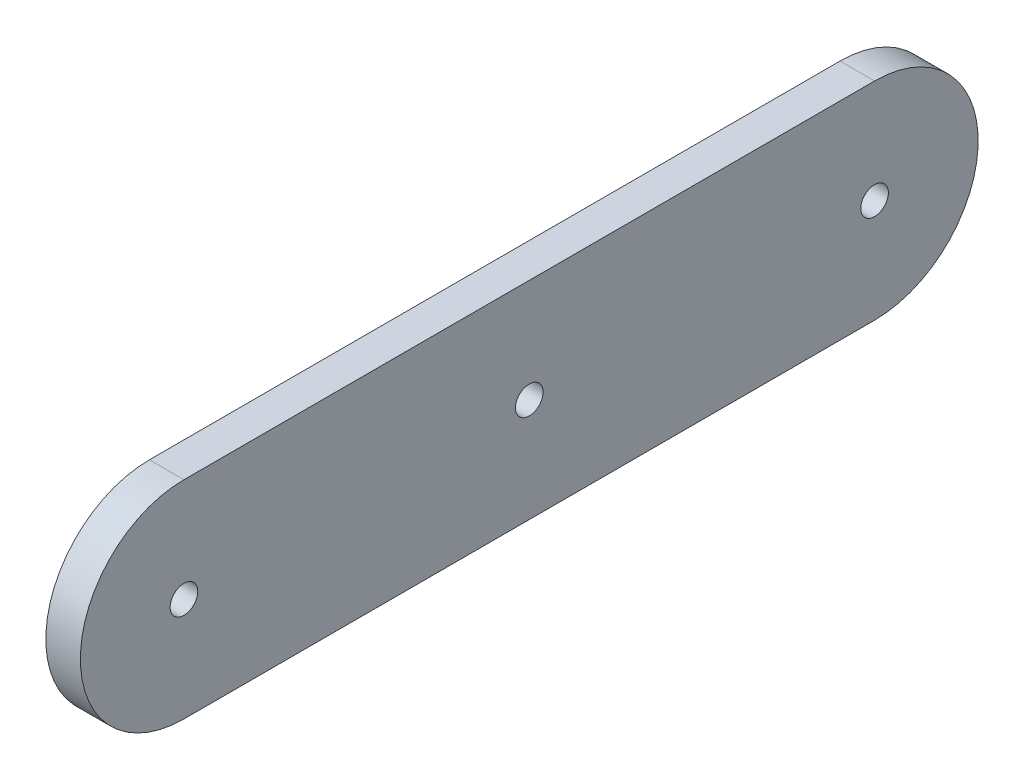
SolidWorks part; units mm, degrees
material "PMMA"
ref_plane "Front Plane" through (0, 0, 0) normal (0, 0, 1) x (1, 0, 0)
ref_plane "Top Plane" through (0, 0, 0) normal (0, 1, 0) x (1, 0, 0)
ref_plane "Right Plane" through (0, 0, 0) normal (1, 0, 0) x (0, 0, -1)
sketch "Schizzo1" plane through (0, 0, 0) normal (1, 0, 0) x (0, 0, -1)
  line L0 (-50, 15) -> (50, -15) construction
  line L1 (-50, 15) -> (50, 15)
  line L2 (-50, 15) -> (-50, -15) construction
  line L3 (-50, -15) -> (50, -15)
  line L4 (50, 15) -> (50, -15) construction
  arc A0 (-50, 15) -> (-50, -15) centre (-50, 0) ccw
  arc A1 (50, 15) -> (50, -15) centre (50, 0) cw
  point P4 (0, 0)
  dimension "D3" = 15
  dimension "D4" = 15
  dimension "D1" = 100
  dimension "D2" = 30
extrude "Estrusione-Estrusione1" add sketch "Schizzo1" along normal blind 5
sketch "Schizzo2" plane through (5, 0, 0) normal (1, 0, 0) x (0, 0, -1)
  circle A0 centre (-50, 0) radius 2
  circle A1 centre (0, 0) radius 2
  circle A2 centre (50, 0) radius 2
  dimension "D1" = 4
extrude "Taglio-Estrusione1" cut sketch "Schizzo2" against normal through all
equation "\"Thickness5\"=5"
equation "\"D1@Estrusione-Estrusione1\"=\"Thickness5\""
